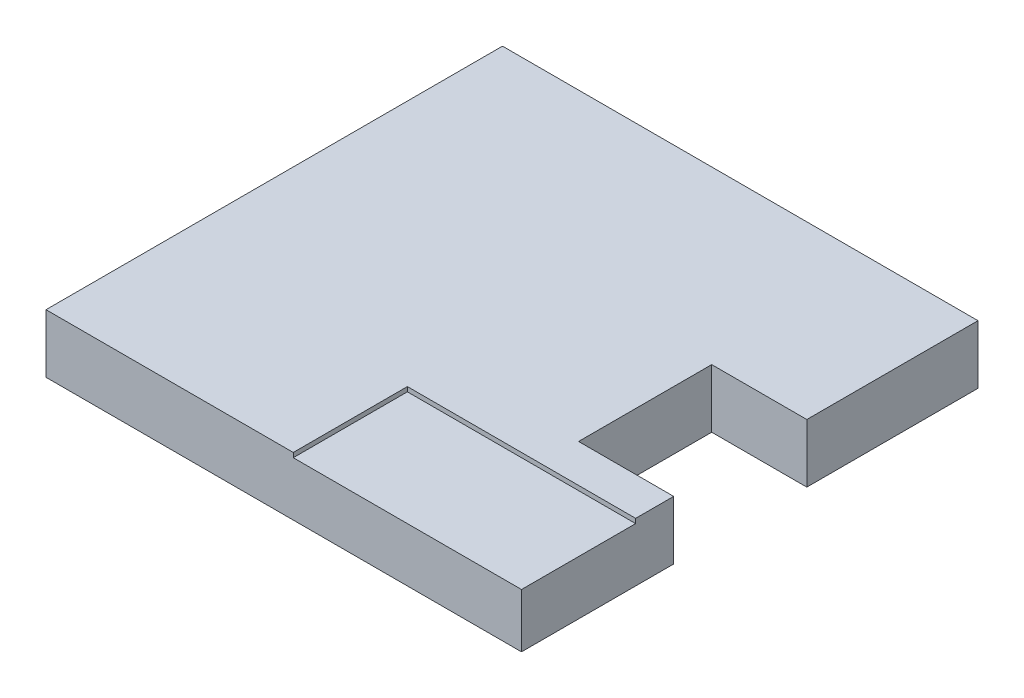
SolidWorks part; units mm, degrees
ref_plane "Front Plane" through (0, 0, 0) normal (0, 0, 1) x (1, 0, 0)
ref_plane "Top Plane" through (0, 0, 0) normal (0, 1, 0) x (1, 0, 0)
ref_plane "Right Plane" through (0, 0, 0) normal (1, 0, 0) x (0, 0, -1)
sketch "Sketch1" plane through (0, 0, 0) normal (0, 1, 0) x (1, 0, 0)
  line L1 (-3.125, 3) -> (3.125, 3)
  line L2 (-3.125, 3) -> (-3.125, -3)
  line L3 (-3.125, -3) -> (3.125, -3)
  line L4 (3.125, 3) -> (3.125, -3)
  point P4 (3.125, 0)
  point P6 (0, -3)
  dimension "D1" = 0
  dimension "D2" = 0
  dimension "D3" = 6
  dimension "D4" = 6.25
extrude "Boss-Extrude1" add sketch "Sketch1" along normal blind 0.71
sketch "Sketch2" plane through (0, 0.71, 0) normal (0, 1, 0) x (1, 0, 0)
  line L0 (3.125, 3) -> (-3.125, 3)
  line L1 (-3.125, 3) -> (-3.125, -3)
  line L2 (-3.125, -3) -> (0.125, -3)
  line L3 (-3.125, -3) -> (3.125, -3) construction
  line L4 (0.125, -3) -> (0.125, -1.5)
  line L5 (0.125, -1.5) -> (3.125, -1.5)
  line L6 (3.125, -3) -> (3.125, 3) construction
  line L7 (3.125, -1.5) -> (3.125, -1)
  line L8 (3.125, -1) -> (1.875, -1)
  line L9 (1.875, -1) -> (1.875, 0.75)
  line L10 (1.875, 0.75) -> (3.125, 0.75)
  line L11 (3.125, 0.75) -> (3.125, 3)
  dimension "D1" = 3
  dimension "D2" = 1.5
  dimension "D3" = 1.25
  dimension "D4" = 1.75
  dimension "D5" = 2.25
extrude "Boss-Extrude2" add sketch "Sketch2" along normal blind 0.06
sketch "Sketch3" plane through (0, 0.71, 0) normal (0, 1, 0) x (1, 0, 0)
  line L1 (3.125, 0.75) -> (1.875, 0.75)
  line L2 (3.125, 0.75) -> (3.125, -1)
  line L3 (3.125, -1) -> (1.875, -1)
  line L4 (1.875, 0.75) -> (1.875, -1)
extrude "Cut-Extrude1" cut sketch "Sketch3" against normal through all
